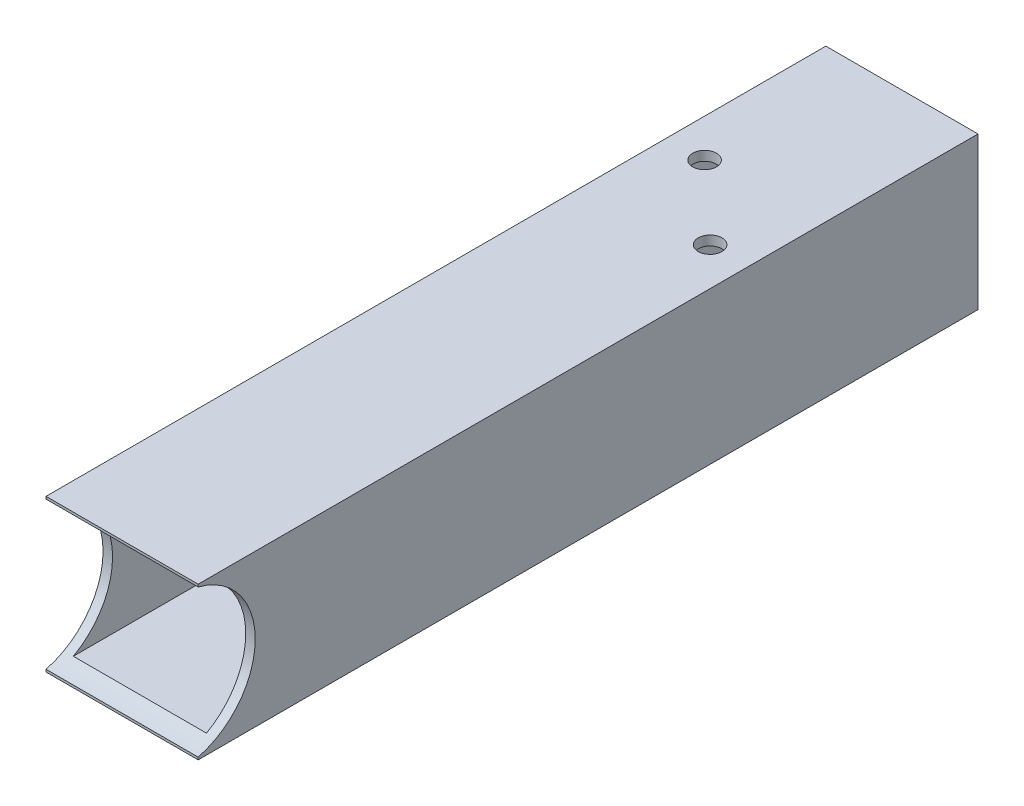
SolidWorks part; units mm, degrees
material "6061-T6 (SS)"
ref_plane "Front Plane" through (0, 0, 0) normal (0, 0, 1) x (1, 0, 0)
ref_plane "Top Plane" through (0, 0, 0) normal (0, 1, 0) x (1, 0, 0)
ref_plane "Right Plane" through (0, 0, 0) normal (1, 0, 0) x (0, 0, -1)
sketch "Sketch1" plane through (0, 0, 0) normal (0, 0, 1) x (1, 0, 0)
  line L0 (3.175, 47.625) -> (47.625, 47.625)
  line L1 (0, 0) -> (50.8, 0)
  line L2 (0, 0) -> (0, 50.8)
  line L3 (0, 50.8) -> (50.8, 50.8)
  line L4 (50.8, 0) -> (50.8, 50.8)
  line L5 (47.625, 3.175) -> (47.625, 47.625)
  line L6 (3.175, 3.175) -> (47.625, 3.175)
  line L7 (3.175, 3.175) -> (3.175, 47.625)
  dimension "D1" = 50.8
  dimension "D2" = 50.8
  dimension "D3" = 3.175
extrude "Boss-Extrude1" add sketch "Sketch1" along normal blind 260.35
sketch "Sketch2" plane through (50.8, 0, 0) normal (1, 0, 0) x (0, 0, -1)
  line L0 (-260.35, 0) -> (-260.35, 50.8) construction
  line L2 (-260.35, 0) -> (0, 0) construction
  circle A0 centre (-266.7, 25.4) radius 25.4
  dimension "D1" = 50.8
  dimension "D2" = 6.35
  dimension "D3" = 25.4
extrude "Cut-Extrude1" cut sketch "Sketch2" against normal through all
sketch "Sketch3" plane through (0, 0, 0) normal (0, -1, 0) x (1, 0, 0)
  line L18 (12.7, 57.1438) -> (12.7, 49.2063) construction
  circle A12 centre (38.1, 76.7358) radius 3.9687
  circle A13 centre (12.7, 53.175) radius 3.9688
  point P0 (38.1, 76.7358)
  point P1 (38.1, 76.7358)
  point P2 (12.7, 53.175)
  point P5 (0, 0)
  point P6 (0, 0)
  point P12 (12.7, 57.1438)
  point P22 (12.7, 49.2063)
  point P23 (38.1, 76.7358)
  point P24 (12.7, 53.175)
  point P25 (38.1, 76.7358)
extrude "Cut-Extrude2" cut sketch "Sketch3" against normal through all
